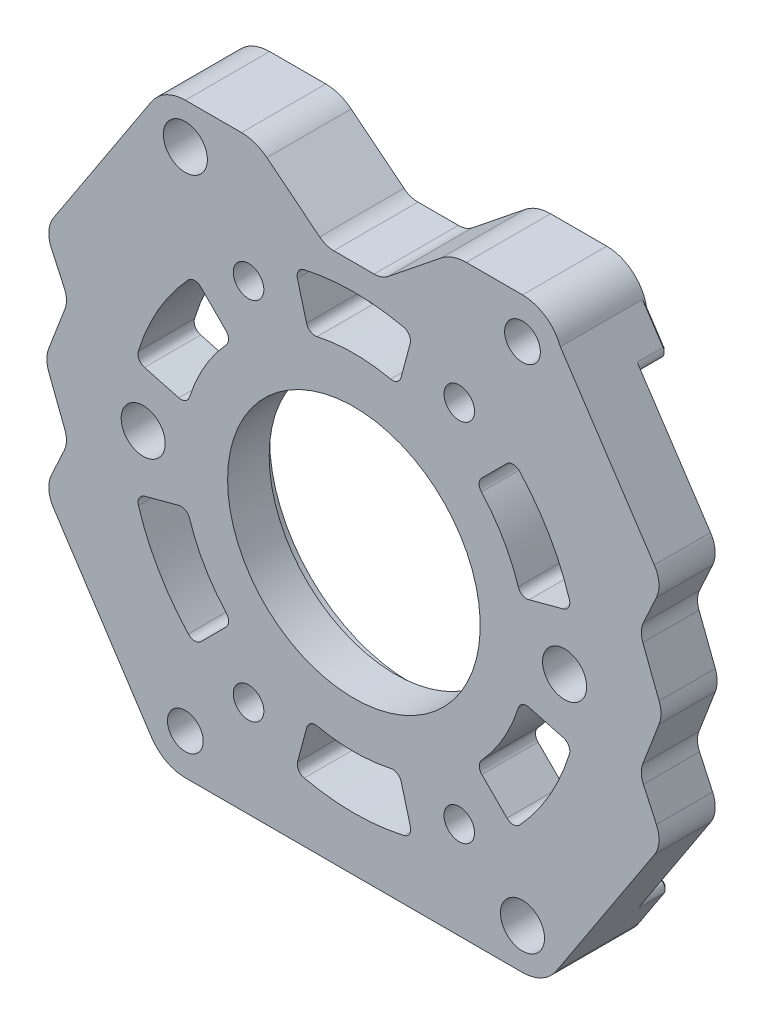
SolidWorks part; units mm, degrees
ref_plane "Front Plane" through (0, 0, 0) normal (0, 0, 1) x (1, 0, 0)
ref_plane "Top Plane" through (0, 0, 0) normal (0, 1, 0) x (1, 0, 0)
ref_plane "Right Plane" through (0, 0, 0) normal (1, 0, 0) x (0, 0, -1)
ref_plane "Plane1" through (0, 0, -1.5875) normal (0, 0, -1) x (-1, 0, 0)
sketch "Sketch1" plane through (0, 0, -1.5875) normal (0, 0, -1) x (-1, 0, 0)
  line L0 (-34.925, -12.7) -> (-21.5281, -33.1597)
  line L1 (-21.5281, -33.1597) -> (21.5281, -33.1597)
  line L2 (21.5281, -33.1597) -> (34.925, -12.7)
  line L3 (34.925, -12.7) -> (32.2643, -6.9343)
  line L4 (32.2643, -6.9343) -> (34.925, 0)
  line L5 (34.925, 0) -> (32.2643, 6.9343)
  line L6 (32.2643, 6.9343) -> (34.925, 12.7)
  line L7 (34.925, 12.7) -> (21.5281, 33.1597)
  line L8 (21.5281, 33.1597) -> (-19.05, 33.1597)
  line L9 (-23.3304, 30.2174) -> (-34.925, 12.7)
  line L10 (-34.925, 12.7) -> (-32.2643, 6.9343)
  line L11 (-32.2643, 6.9343) -> (-34.925, 0)
  line L12 (-34.925, 0) -> (-32.2643, -6.9343)
  line L13 (-32.2643, -6.9343) -> (-34.925, -12.7)
  line L14 (-6.6489, -26.2054) -> (-5.096, -20.4098)
  line L15 (5.0715, -20.4165) -> (6.6244, -26.212)
  arc A0 (-19.05, 33.1597) -> (-23.3304, 30.2174) centre (-19.05, 28.575) ccw
  arc A1 (6.6244, -26.212) -> (-6.6489, -26.2054) centre (0, -1.5875) cw
  arc A2 (-5.096, -20.4098) -> (5.0715, -20.4165) centre (0, -1.5875) ccw
extrude "Boss-Extrude1" add sketch "Sketch1" against normal blind 6.35
sketch "Sketch2" plane through (0, 0, -1.5875) normal (0, 0, -1) x (-1, 0, 0)
  line L0 (25.7631, -26.6921) -> (21.5281, -33.1597)
  line L1 (21.5281, -33.1597) -> (-21.5281, -33.1597)
  line L2 (-21.5281, -33.1597) -> (-25.7631, -26.6921)
  line L3 (-25.099, -25.4635) -> (-6.4501, -25.4635)
  line L4 (-6.4501, -25.4635) -> (-6.6489, -26.2054)
  line L5 (6.6244, -26.212) -> (6.4239, -25.4635)
  line L6 (6.4239, -25.4635) -> (25.099, -25.4635)
  arc A0 (25.099, -25.4635) -> (25.7631, -26.6921) centre (25.099, -26.2572) cw
  arc A1 (-25.7631, -26.6921) -> (-25.099, -25.4635) centre (-25.099, -26.2572) cw
  arc A2 (-6.6489, -26.2054) -> (6.6244, -26.212) centre (0, -1.5875) ccw
extrude "Boss-Extrude2" add sketch "Sketch2" along normal blind 3.175
sketch "Sketch3" plane through (0, 0, -1.5875) normal (0, 0, -1) x (-1, 0, 0)
  line L0 (25.099, 25.4635) -> (-24.9997, 25.4635)
  line L1 (-25.6616, 26.6954) -> (-23.3304, 30.2174)
  line L2 (-19.05, 33.1597) -> (21.5281, 33.1597)
  line L3 (21.5281, 33.1597) -> (25.7631, 26.6921)
  arc A0 (25.7631, 26.6921) -> (25.099, 25.4635) centre (25.099, 26.2572) cw
  arc A1 (-24.9997, 25.4635) -> (-25.6616, 26.6954) centre (-24.9997, 26.2572) cw
  arc A2 (-23.3304, 30.2174) -> (-19.05, 33.1597) centre (-19.05, 28.575) cw
extrude "Boss-Extrude3" add sketch "Sketch3" along normal blind 3.175
sketch "Sketch4" plane through (0, 0, 4.7625) normal (0, 0, 1) x (1, 0, 0)
  line L0 (3.175, 33.1597) -> (-3.175, 33.1597)
  line L1 (-3.175, 33.1597) -> (-3.175, 26.8097)
  line L2 (-3.175, 26.8097) -> (3.175, 26.8097)
  line L3 (3.175, 26.8097) -> (3.175, 33.1597)
extrude "Cut-Extrude1" cut sketch "Sketch4" against normal through all
sketch "Sketch5" plane through (0, 0, -1.5875) normal (0, 0, -1) x (-1, 0, 0)
  line L0 (18.8486, 3.4104) -> (24.6442, 4.9633)
  line L1 (18.0133, 16.4617) -> (13.7706, 12.219)
  arc A0 (13.7706, 12.219) -> (18.8486, 3.4104) centre (0, -1.5875) cw
  arc A1 (24.6442, 4.9633) -> (18.0133, 16.4617) centre (0, -1.5875) ccw
extrude "Cut-Extrude2" cut sketch "Sketch5" against normal through all
sketch "Sketch6" plane through (0, 0, -1.5875) normal (0, 0, -1) x (-1, 0, 0)
  line L0 (-24.6377, 4.9878) -> (-18.8421, 3.4349)
  line L1 (-13.7526, 12.237) -> (-17.9953, 16.4796)
  arc A0 (-17.9953, 16.4796) -> (-24.6377, 4.9878) centre (0, -1.5875) ccw
  arc A1 (-18.8421, 3.4349) -> (-13.7526, 12.237) centre (0, -1.5875) cw
extrude "Cut-Extrude3" cut sketch "Sketch6" against normal through all
sketch "Sketch7" plane through (0, 0, -1.5875) normal (0, 0, -1) x (-1, 0, 0)
  line L0 (-18.0133, -19.6367) -> (-13.7706, -15.394)
  line L1 (-18.8486, -6.5854) -> (-24.6442, -8.1383)
  arc A0 (-24.6442, -8.1383) -> (-18.0133, -19.6367) centre (0, -1.5875) ccw
  arc A1 (-13.7706, -15.394) -> (-18.8486, -6.5854) centre (0, -1.5875) cw
extrude "Cut-Extrude4" cut sketch "Sketch7" against normal through all
sketch "Sketch8" plane through (0, 0, -1.5875) normal (0, 0, -1) x (-1, 0, 0)
  line L0 (-6.6244, 23.037) -> (-5.0715, 17.2415)
  line L1 (5.096, 17.2348) -> (6.6489, 23.0304)
  arc A0 (6.6489, 23.0304) -> (-6.6244, 23.037) centre (0, -1.5875) ccw
  arc A1 (-5.0715, 17.2415) -> (5.096, 17.2348) centre (0, -1.5875) cw
extrude "Cut-Extrude5" cut sketch "Sketch8" against normal through all
sketch "Sketch9" plane through (0, 0, 4.7625) normal (0, 0, 1) x (1, 0, 0)
  line L0 (-18.8421, -6.6099) -> (-24.6377, -8.1628)
  line L1 (-17.9953, -19.6546) -> (-13.7526, -15.412)
  arc A0 (-24.6377, -8.1628) -> (-17.9953, -19.6546) centre (0, -1.5875) ccw
  arc A1 (-13.7526, -15.412) -> (-18.8421, -6.6099) centre (0, -1.5875) cw
extrude "Cut-Extrude6" cut sketch "Sketch9" against normal through all
draft "Draft1" type of draft neutral plane draft angle 51.253 faces to draft 2 face at (-3.175, 29.9847, 0) face at (3.175, 29.9847, 0) neutral plane through (-3.175, 26.8097, -4.7625) neutral plane normal (0, 1, 0) parameters "D1"=51.253
hole_wizard "Hole1" positions "Sketch11" profile "Sketch10" legacy
sketch "Sketch11" plane through (0, 0, -4.7625) normal (0, 0, -1) x (-1, 0, 0)
  point P0 (-19.05, -28.575)
  point P1 (19.05, 28.575)
sketch "Sketch10" plane through (19.05, -28.575, -4.7625) normal (1, 0, 0) x (0, 1, 0)
  line L0 (0, 0) -> (0, 9.525)
  line L1 (0, 9.525) -> (2.4892, 9.525)
  line L2 (2.4892, 9.525) -> (2.4892, 0)
  line L3 (2.4892, 0) -> (0, 0)
  line L4 (0, 110) -> (0, -10) construction
  dimension "Diameter" = 4.9784
  dimension "Depth" = 9.525
hole_wizard "M3 Clearance Hole1" positions "Sketch13" profile "Sketch12" hole size "M3" standard "ANSI Metric"
sketch "Sketch13" plane through (0, 0, -1.5875) normal (0, 0, -1) x (-1, 0, 0)
  point P0 (11.9063, 19.0347)
  point P1 (-11.9062, 19.0347)
  point P2 (-11.9063, -22.2097)
  point P3 (11.9062, -22.2097)
sketch "Sketch12" plane through (-11.9063, 19.0347, -1.5875) normal (1, 0, 0) x (0, 1, 0)
  line L0 (0, 0) -> (0, 6.35)
  line L1 (0, 6.35) -> (1.7272, 6.35)
  line L2 (1.7272, 6.35) -> (1.7272, 0)
  line L5 (1.7272, 0) -> (0, 0)
  line L11 (0, -6.35) -> (0, 107.95) construction
  dimension "Thru Hole Dia." = 3.4544
  dimension "Thru Hole Depth" = 6.35
hole_wizard "M3.5 Clearance Hole1" positions "Sketch15" profile "Sketch14" hole size "M3.5" standard "ANSI Metric"
sketch "Sketch15" plane through (0, 0, -4.7625) normal (0, 0, -1) x (-1, 0, 0)
  point P0 (-19.05, 28.575)
  point P1 (19.05, -28.575)
sketch "Sketch14" plane through (19.05, 28.575, -4.7625) normal (1, 0, 0) x (0, 1, 0)
  line L0 (0, 0) -> (0, 9.525)
  line L1 (0, 9.525) -> (2.0193, 9.525)
  line L2 (2.0193, 9.525) -> (2.0193, 0)
  line L5 (2.0193, 0) -> (0, 0)
  line L11 (0, -6.35) -> (0, 107.95) construction
  dimension "Thru Hole Dia." = 4.0386
  dimension "Thru Hole Depth" = 9.525
hole_wizard "Hole2" positions "Sketch17" profile "Sketch16" legacy
sketch "Sketch17" plane through (0, 0, -1.5875) normal (0, 0, -1) x (-1, 0, 0)
  point P0 (23.8125, -1.5875)
  point P1 (-23.8125, -1.5875)
sketch "Sketch16" plane through (-23.8125, -1.5875, -1.5875) normal (1, 0, 0) x (0, 1, 0)
  line L0 (0, 0) -> (0, 6.35)
  line L1 (0, 6.35) -> (2.4892, 6.35)
  line L2 (2.4892, 6.35) -> (2.4892, 0)
  line L3 (2.4892, 0) -> (0, 0)
  line L4 (0, 110) -> (0, -10) construction
  dimension "Diameter" = 4.9784
  dimension "Depth" = 6.35
hole_wizard "CBORE for M25 SHSS1" positions "Sketch19" profile "Sketch18" counterbore size "M25" standard "ANSI Metric"
sketch "Sketch19" plane through (0, 0, -1.5875) normal (0, 0, -1) x (-1, 0, 0)
  point P0 (0, -1.5875)
sketch "Sketch18" plane through (0, -1.5875, -1.5875) normal (1, 0, 0) x (0, 1, 0)
  line L0 (0, 0) -> (0, 6.35)
  line L1 (0, 6.35) -> (14.2748, 6.35)
  line L3 (14.2748, 6.35) -> (14.2748, 1.651)
  line L4 (14.2748, 1.651) -> (15.875, 1.651)
  line L5 (15.875, 1.651) -> (15.875, 0)
  line L7 (15.875, 0) -> (0, 0)
  line L11 (0, -6.35) -> (0, 107.95) construction
  dimension "Thru Hole Dia." = 28.5496
  dimension "Thru Hole Depth" = 6.35
  dimension "C'Bore Dia." = 31.75
  dimension "C'Bore Depth" = 1.651
cosmetic thread "Hole Thread1" parameters "D1"=0, "D2"=29.5496
chamfer "Chamfer1" distance 0.25 angle 45 11 edges at (-23.6456, -29.9259, -4.7625) (-25.7973, -25.8798, -4.7625) (-15.7614, -25.4635, -4.7625) (24.496, 28.4564, -4.7625) (-23.6456, 29.9259, -4.7625) (25.6989, 25.8816, -4.7625) (-25.7973, 25.8798, -4.7625) (-0.0496, 25.4635, -4.7625) (23.6456, -29.9259, -4.7625) (25.7973, -25.8798, -4.7625) (15.7746, -25.4635, -4.7625)
fillet "Fillet1" radius 1 24 edges at (-24.6377, -8.1628, 1.5875) (18.8421, 3.4349, 1.5875) (5.0715, 17.2415, 1.5875) (-5.0715, -20.4165, 1.5875) (13.7526, 12.237, 1.5875) (-17.9953, -19.6546, 1.5875) (-13.7526, -15.412, 1.5875) (-6.6244, -26.212, 0) (24.6377, 4.9878, 1.5875) (6.6489, -26.2054, 0) (17.9953, 16.4796, 1.5875) (-18.0133, 16.4617, 1.5875) (6.6244, 23.037, 1.5875) (18.0133, -19.6367, 1.5875) (-18.8421, -6.6099, 1.5875) (13.7706, -15.394, 1.5875) (5.096, -20.4098, 1.5875) (24.6442, -8.1383, 1.5875) (18.8486, -6.5854, 1.5875) (-24.6442, 4.9633, 1.5875) (-13.7706, 12.219, 1.5875) (-6.6489, 23.0304, 1.5875) (-18.8486, 3.4104, 1.5875) (-5.096, 17.2348, 1.5875)
fillet "Fillet2" radius 2.54 6 edges at (-32.2643, 6.9343, 1.5875) (32.2643, -6.9343, 1.5875) (32.2643, 6.9343, 1.5875) (3.175, 26.8097, 0) (-3.175, 26.8097, 0) (-32.2643, -6.9343, 1.5875)
fillet "Fillet3" radius 3.175 6 edges at (-34.925, 0, 1.5875) (34.925, 12.7, 1.5875) (34.925, 0, 1.5875) (-34.925, -12.7, 1.5875) (-34.925, 12.7, 1.5875) (34.925, -12.7, 1.5875)
fillet "Fillet4" radius 4.5847 5 edges at (11.0879, 33.1597, 0) (-21.5281, 33.1597, 0.125) (-11.0879, 33.1597, 0) (21.5281, -33.1597, 0.125) (-21.5281, -33.1597, 0.125)
